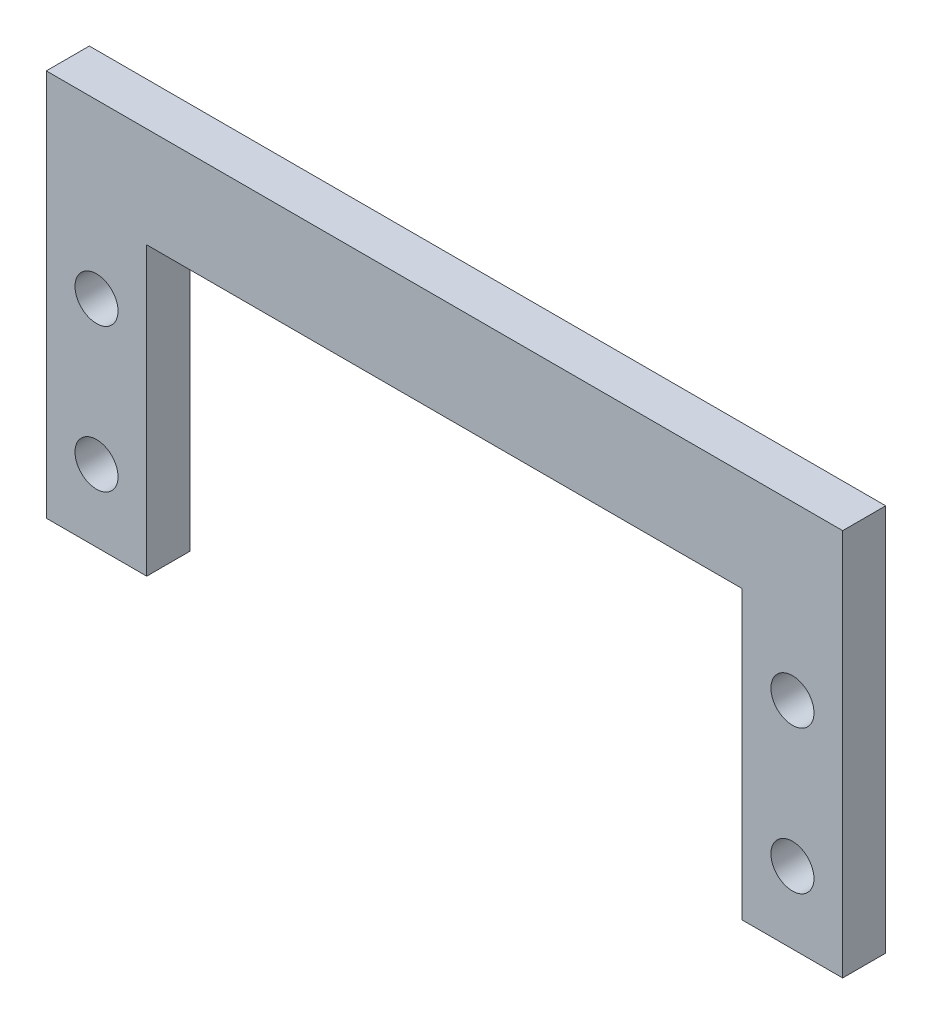
SolidWorks part; units mm, degrees
material "PVC hart"
ref_plane "Ebene vorne" through (0, 0, 0) normal (0, 0, 1) x (1, 0, 0)
ref_plane "Ebene oben" through (0, 0, 0) normal (0, 1, 0) x (1, 0, 0)
ref_plane "Ebene rechts" through (0, 0, 0) normal (1, 0, 0) x (0, 0, -1)
sketch "Skizze3" plane through (0, 0, 0) normal (0, 0, 1) x (1, 0, 0)
  line L1 (-30.75, 10) -> (10.75, 10)
  line L2 (-30.75, 10) -> (-30.75, -10)
  line L4 (10.75, 10) -> (10.75, -10)
  line L5 (-34.25, 5) -> (-34.25, -5) construction
  line L6 (14.25, 5) -> (14.25, -5) construction
  line L7 (-34.25, 0) -> (-30.75, 0) construction
  line L8 (10.75, 0) -> (14.25, 0) construction
  line L9 (-30.75, 0) -> (0, 0) construction
  line L10 (0, 0) -> (10.75, 0) construction
  line L13 (-30.75, -10) -> (-37.75, -10)
  line L14 (-37.75, -10) -> (-37.75, 17)
  line L15 (-37.75, 17) -> (17.75, 17)
  line L16 (17.75, 17) -> (17.75, -10)
  line L17 (17.75, -10) -> (10.75, -10)
  circle A0 centre (-34.25, 5) radius 1.5
  circle A1 centre (-34.25, -5) radius 1.5
  circle A2 centre (14.25, 5) radius 1.5
  circle A3 centre (14.25, -5) radius 1.5
  point P18 (0, 0)
  dimension "D2" = 3
  dimension "D1" = 10
  dimension "D3" = 48.5
  dimension "D4" = 41.5
  dimension "D5" = 20
  dimension "D6" = 14.25
  dimension "D7" = 7
  dimension "D8" = 7
extrude "Aufsatz-Linear austragen1" add sketch "Skizze3" along normal mid plane 3
